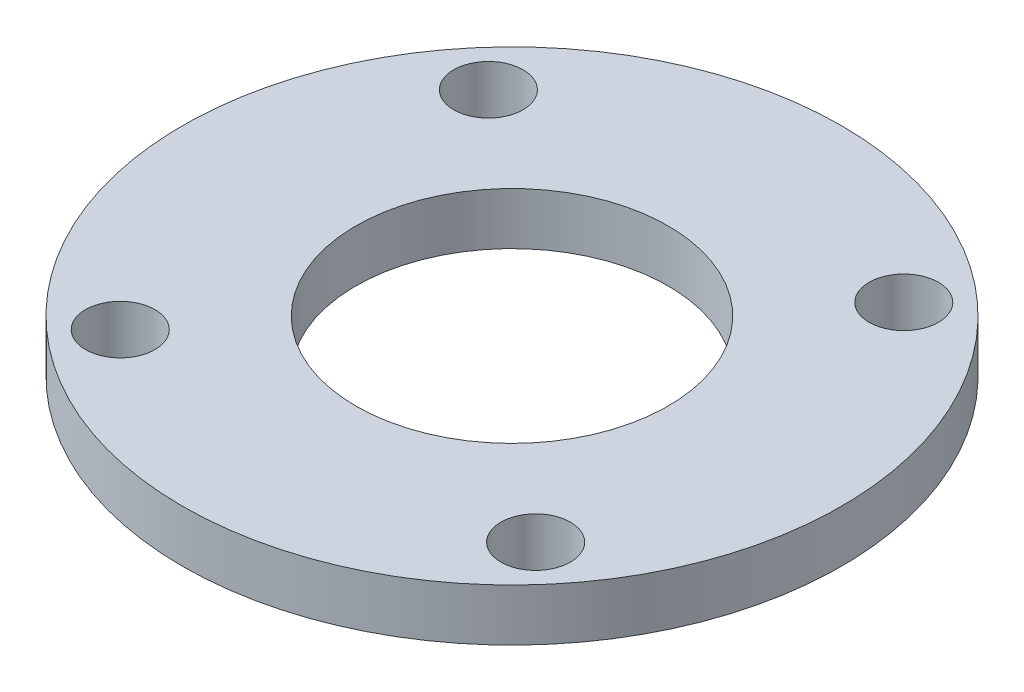
SolidWorks part; units mm, degrees
ref_plane "Front Plane" through (0, 0, 0) normal (0, 0, 1) x (1, 0, 0)
ref_plane "Top Plane" through (0, 0, 0) normal (0, 1, 0) x (1, 0, 0)
ref_plane "Right Plane" through (0, 0, 0) normal (1, 0, 0) x (0, 0, -1)
sketch "Sketch1" plane through (0, 0, 0) normal (0, 1, 0) x (1, 0, 0)
  circle A0 centre (0, 0) radius 19
  dimension "D1" = 38
extrude "Boss-Extrude1" add sketch "Sketch1" along normal blind 3
sketch "Sketch2" plane through (0, 3, 0) normal (0, 1, 0) x (1, 0, 0)
  circle A0 centre (-11.9745, 10.6119) radius 2
  circle A1 centre (10.6119, 11.9745) radius 2
  circle A2 centre (11.9745, -10.6119) radius 2
  circle A3 centre (-10.6119, -11.9745) radius 2
  point P12 (0, 0)
  dimension "D1" = 4
  dimension "D2" = 16
  dimension "D3" = 4
extrude "Cut-Extrude1" cut sketch "Sketch2" against normal blind 3
sketch "Sketch3" plane through (0, 3, 0) normal (0, 1, 0) x (1, 0, 0)
  circle A0 centre (0, 0) radius 9
  dimension "D1" = 18
extrude "Cut-Extrude2" cut sketch "Sketch3" against normal blind 3
